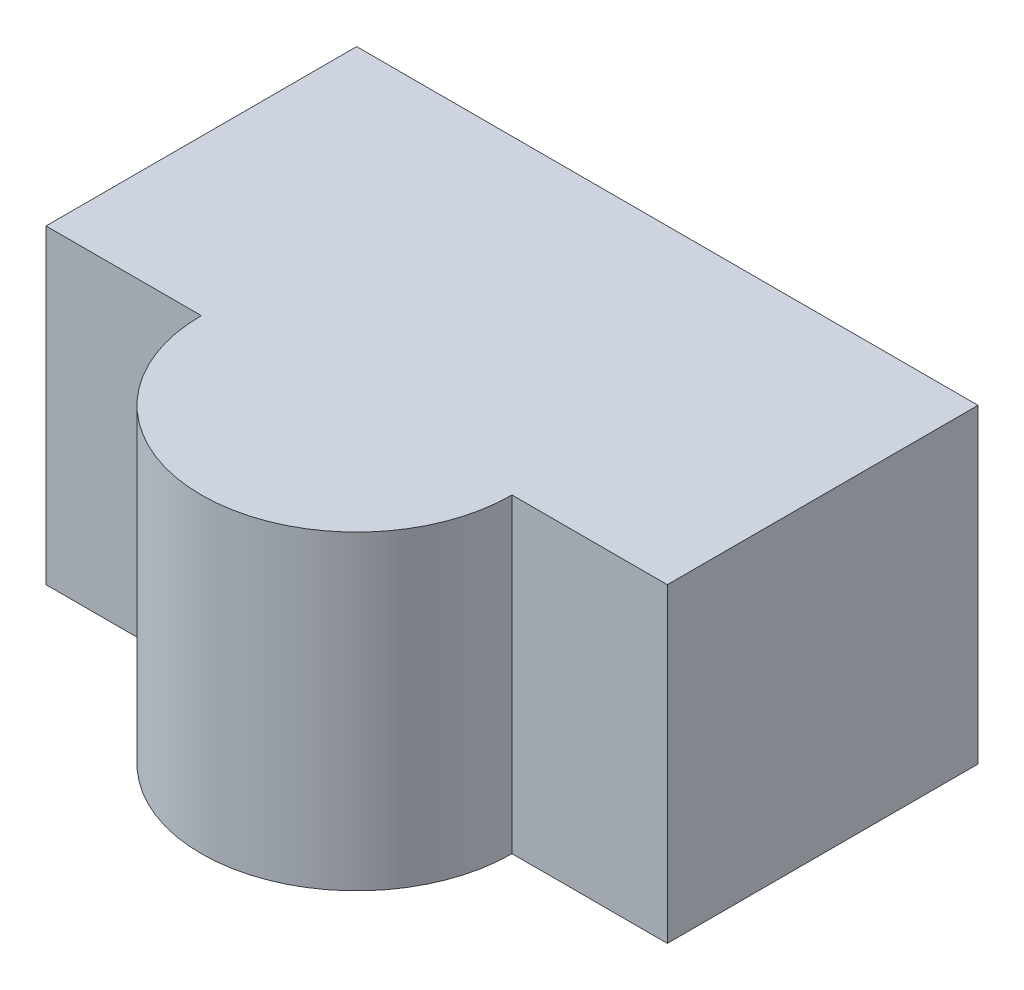
SolidWorks part; units mm, degrees
ref_plane "Alzado" through (0, 0, 0) normal (0, 0, 1) x (1, 0, 0)
ref_plane "Planta" through (0, 0, 0) normal (0, 1, 0) x (1, 0, 0)
ref_plane "Vista lateral" through (0, 0, 0) normal (1, 0, 0) x (0, 0, -1)
sketch "Croquis1" plane through (0, 0, 0) normal (0, 1, 0) x (1, 0, 0)
  line L1 (-20, 10) -> (20, 10)
  line L2 (-20, 10) -> (-20, -10)
  line L3 (-20, -10) -> (20, -10)
  line L4 (20, 10) -> (20, -10)
  line L5 (-20, 10) -> (20, -10) construction
  line L6 (-20, -10) -> (20, 10) construction
  point P0 (0, 0)
  dimension "D1" = 40
  dimension "D2" = 20
extrude "Saliente-Extruir1" add sketch "Croquis1" along normal blind 20
sketch "Croquis2" plane through (0, 20, 0) normal (0, 1, 0) x (1, 0, 0)
  line L0 (-20, -10) -> (20, -10) construction
  line L1 (-10, -10) -> (10, -10)
  arc A0 (-10, -10) -> (10, -10) centre (0, -10) ccw
extrude "Saliente-Extruir2" add sketch "Croquis2" against normal blind 20
